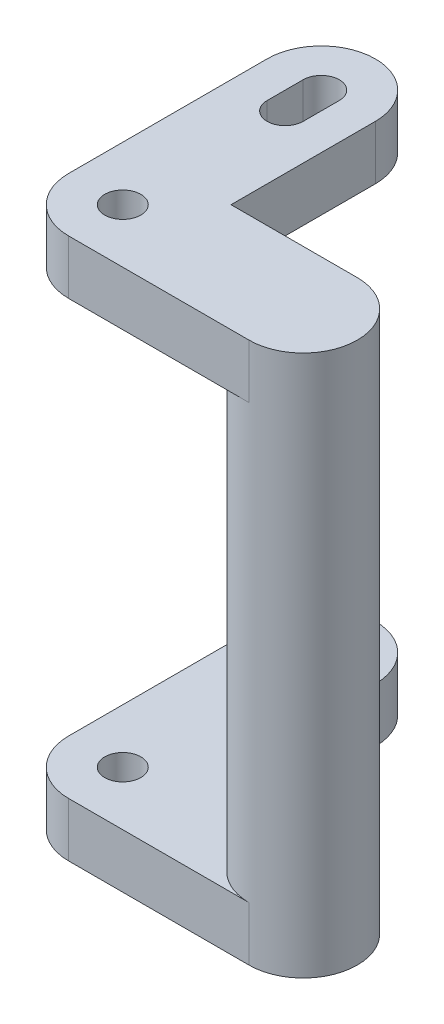
SolidWorks part; units mm, degrees
ref_plane "Front Plane" through (0, 0, 0) normal (0, 0, 1) x (1, 0, 0)
ref_plane "Top Plane" through (0, 0, 0) normal (0, 1, 0) x (1, 0, 0)
ref_plane "Right Plane" through (0, 0, 0) normal (1, 0, 0) x (0, 0, -1)
sketch "Sketch1" plane through (0, 0, 0) normal (0, 1, 0) x (1, 0, 0)
  line L0 (5, -1) -> (1.5, -1)
  line L2 (-1.5, 2.5) -> (-1.5, -2.5)
  line L4 (1.5, 2.5) -> (1.5, -1)
  line L5 (-1.5, 2.5) -> (1.5, -2.5) construction
  line L6 (-1.5, -2.5) -> (1.5, 2.5) construction
  line L7 (5, -4) -> (0, -4)
  line L8 (5, -1) -> (0, -4) construction
  line L9 (0, -1) -> (5, -4) construction
  line L10 (0, -2.5) -> (1.5, -2.5) construction
  line L11 (0, -2.5) -> (0, -4) construction
  line L12 (-0.5, 3) -> (-0.5, 2)
  line L13 (0.5, 3) -> (0.5, 2)
  line L14 (-1.5, 2.5) -> (-1.5, 3)
  line L15 (1.5, 3) -> (1.5, 2.5)
  arc A1 (-1.5, -2.5) -> (0, -4) centre (0, -2.5) ccw
  circle A2 centre (0, -2.5) radius 0.5
  arc A4 (5, -4) -> (5, -1) centre (5, -2.5) ccw
  arc A8 (0.5, 3) -> (-0.5, 3) centre (0, 3) ccw
  arc A9 (-0.5, 2) -> (0.5, 2) centre (0, 2) ccw
  arc A10 (1.5, 3) -> (-1.5, 3) centre (0, 3) ccw
  point P0 (0, 0)
  point P12 (2.5, -2.5)
  dimension "D3" = 1
  dimension "D1" = 3
  dimension "D2" = 5
  dimension "D6" = 90
  dimension "D5" = 2
extrude "Boss-Extrude1" add sketch "Sketch1" along normal blind 1.5
sketch "Sketch2" plane through (0, 1.5, 0) normal (0, 1, 0) x (1, 0, 0)
  circle A0 centre (5, -2.5) radius 1.5
  dimension "D1" = 3
extrude "Boss-Extrude2" add sketch "Sketch2" along normal blind 12
sketch "Sketch3" plane through (0, 13.5, 0) normal (0, 1, 0) x (1, 0, 0)
  line L0 (1.5, -1) -> (5, -1)
  line L1 (5, -4) -> (0, -4)
  line L2 (-1.5, -2.5) -> (-1.5, 2.5)
  line L3 (1.5, 2.5) -> (1.5, -1)
  line L4 (-0.5, 3) -> (-0.5, 2)
  line L5 (0.5, 3) -> (0.5, 2)
  line L6 (-1.5, 3) -> (-1.5, 2.5)
  line L7 (1.5, 3) -> (1.5, 2.5)
  arc A0 (5, -1) -> (5, -4) centre (5, -2.5) cw
  arc A1 (0, -4) -> (-1.5, -2.5) centre (0, -2.5) cw
  circle A4 centre (0, -2.5) radius 0.5
  arc A5 (0.5, 3) -> (-0.5, 3) centre (0, 3) ccw
  arc A6 (-0.5, 2) -> (0.5, 2) centre (0, 2) ccw
  arc A7 (1.5, 3) -> (-1.5, 3) centre (0, 3) ccw
extrude "Boss-Extrude3" add sketch "Sketch3" along normal blind 1.5
